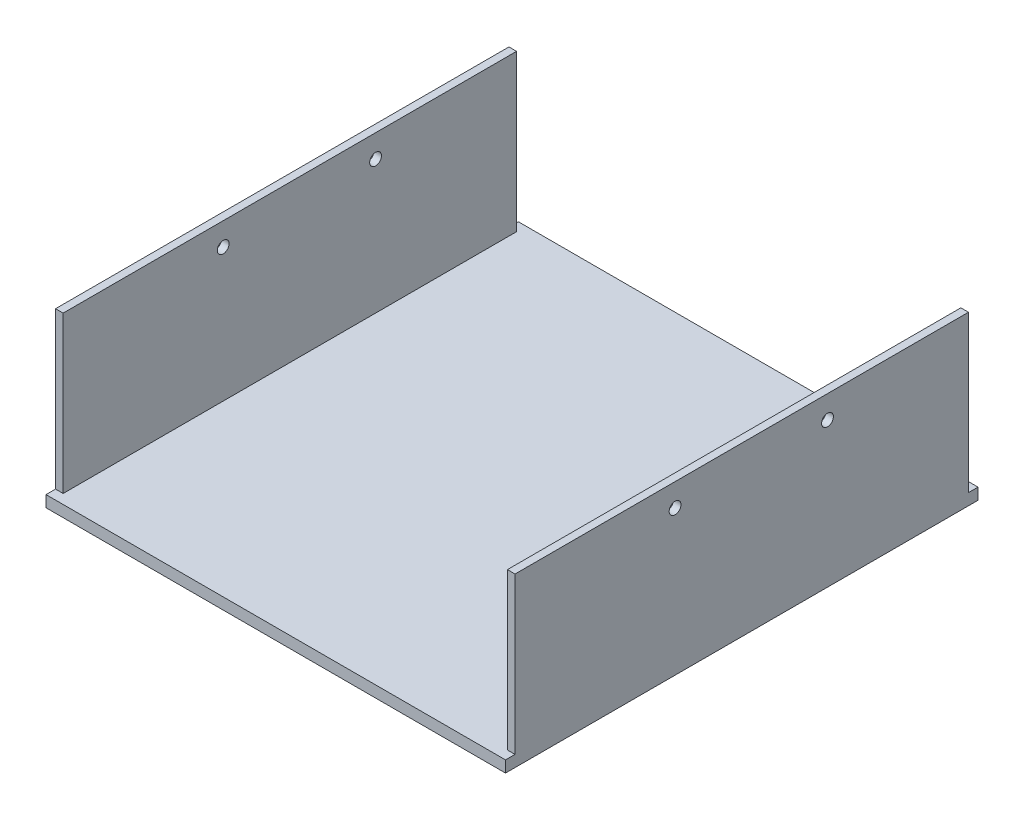
SolidWorks part; units mm, degrees
ref_plane "Front Plane" through (0, 0, 0) normal (0, 0, 1) x (1, 0, 0)
ref_plane "Top Plane" through (0, 0, 0) normal (0, 1, 0) x (1, 0, 0)
ref_plane "Right Plane" through (0, 0, 0) normal (1, 0, 0) x (0, 0, -1)
sketch "Sketch3" plane through (0, 0, 0) normal (0, 1, 0) x (1, 0, 0)
  line L1 (-60.3, 62) -> (60.3, 62)
  line L2 (-60.3, 62) -> (-60.3, -62)
  line L3 (-60.3, -62) -> (60.3, -62)
  line L4 (60.3, 62) -> (60.3, -62)
  line L5 (-60.3, 62) -> (60.3, -62) construction
  line L6 (-60.3, -62) -> (60.3, 62) construction
  point P0 (0, 0)
  dimension "D1" = 124
  dimension "D2" = 120.6
extrude "Boss-Extrude3" add sketch "Sketch3" along normal blind 44
ref_plane "Plane2" through (0, 3, 0) normal (0, 1, 0) x (1, 0, 0)
sketch "Sketch9" plane through (0, 3, 0) normal (0, 1, 0) x (1, 0, 0)
  line L0 (-58.3, 62) -> (-58.3, -62)
  line L1 (60.3, 62) -> (-60.3, 62) construction
  line L2 (-60.3, -62) -> (60.3, -62) construction
  line L3 (-58.3, -62) -> (58.3, -62)
  line L4 (58.3, -62) -> (58.3, 62)
  line L5 (58.3, 62) -> (-58.3, 62)
  line L6 (-60.3, 62) -> (-60.3, -62) construction
  line L7 (60.3, -62) -> (60.3, 62) construction
  dimension "D1" = 2
  dimension "D2" = 2
  dimension "D3" = 116.6
extrude "Cut-Extrude2" cut sketch "Sketch9" along normal through all
sketch "Sketch10" plane through (0, 3, 0) normal (0, 1, 0) x (1, 0, 0)
  line L0 (-60.3, 59.5) -> (60.3, 59.5)
  line L1 (-60.3, 62) -> (-60.3, -62) construction
  line L2 (60.3, -62) -> (60.3, 62) construction
  line L3 (60.3, 59.5) -> (60.3, 62)
  line L4 (60.3, 62) -> (-60.3, 62)
  line L5 (-60.3, 62) -> (-60.3, 59.5)
  dimension "D1" = 2.5
extrude "Cut-Extrude3" cut sketch "Sketch10" along normal through all
sketch "Sketch11" plane through (0, 3, 0) normal (0, 1, 0) x (1, 0, 0)
  line L0 (-60.3, -59.5) -> (60.3, -59.5)
  line L1 (-60.3, 59.5) -> (-60.3, -62) construction
  line L2 (60.3, -62) -> (60.3, 59.5) construction
  line L3 (60.3, -59.5) -> (60.3, -62)
  line L4 (60.3, -62) -> (-60.3, -62)
  line L5 (-60.3, -62) -> (-60.3, -59.5)
  dimension "D1" = 2.5
extrude "Cut-Extrude4" cut sketch "Sketch11" along normal through all
ref_plane "Plane3" through (-63.3, 0, 0) normal (-1, 0, 0) x (0, 0, 1)
sketch "Sketch12" plane through (-63.3, 0, 0) normal (-1, 0, 0) x (0, 0, 1)
  line L0 (-79.6941, 38) -> (85.8459, 38) construction
  line L1 (-59.5, 44) -> (59.5, 44) construction
  line L2 (-59.5, 44) -> (-59.5, 3) construction
  circle A0 centre (-22.5, 38) radius 1.55
  circle A1 centre (17.5, 38) radius 1.55
  dimension "D4" = 3.1
  dimension "D5" = 3.1
  dimension "D1" = 6
  dimension "D2" = 37
  dimension "D3" = 40
extrude "Cut-Extrude5" cut sketch "Sketch12" against normal through all
